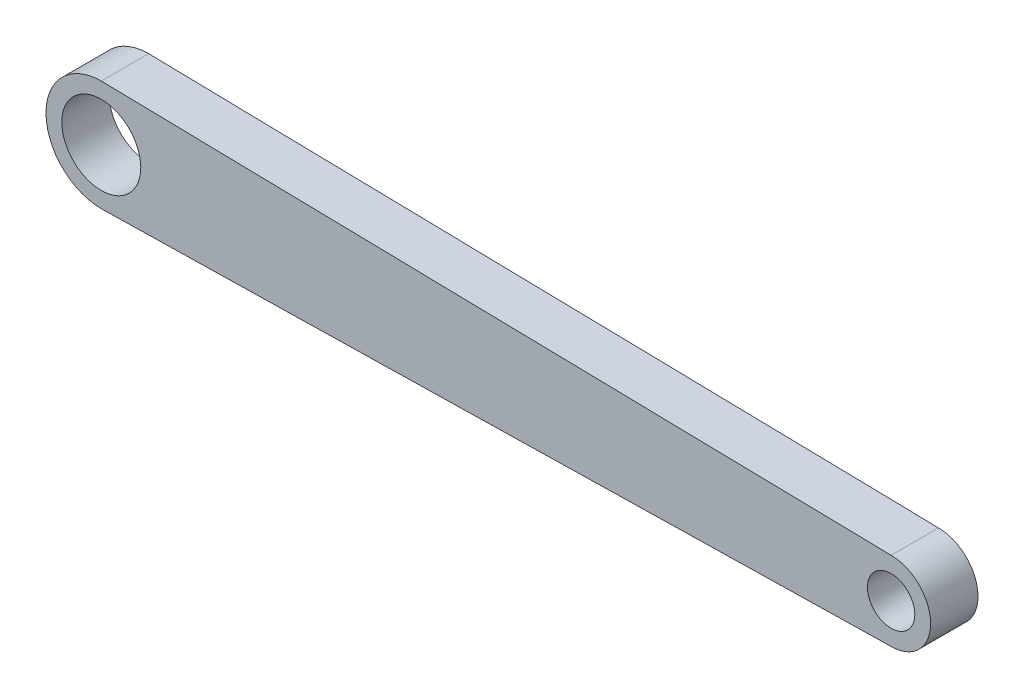
SolidWorks part; units mm, degrees
ref_plane "Front Plane" through (0, 0, 0) normal (0, 0, 1) x (1, 0, 0)
ref_plane "Top Plane" through (0, 0, 0) normal (0, 1, 0) x (1, 0, 0)
ref_plane "Right Plane" through (0, 0, 0) normal (1, 0, 0) x (0, 0, -1)
sketch "Sketch1" plane through (0, 0, 0) normal (0, 0, 1) x (1, 0, 0)
  line L0 (0, 0) -> (50, 0) construction
  line L1 (0, 3.5) -> (50, 2.5)
  line L2 (0, -3.5) -> (50, -2.5)
  arc A0 (0.1399, 3.4972) -> (0.1399, -3.4972) centre (0, 0) ccw
  circle A1 centre (0, 0) radius 2.5
  arc A2 (50, -2.5) -> (50, 2.5) centre (50, 0) ccw
  circle A3 centre (50, 0) radius 1.5
  dimension "D1" = 7
  dimension "D2" = 5
  dimension "D3" = 5
  dimension "D4" = 3
  dimension "D5" = 50
extrude "Boss-Extrude1" add sketch "Sketch1" along normal blind 3
